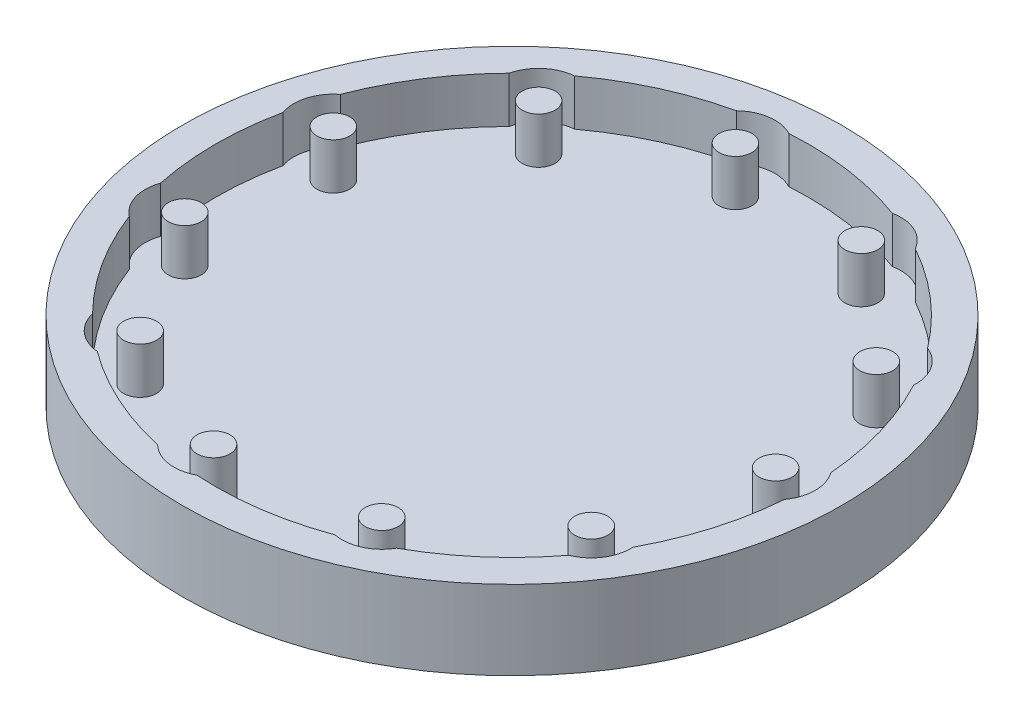
SolidWorks part; units mm, degrees
material "PET"
ref_plane "Front Plane" through (0, 0, 0) normal (0, 0, 1) x (1, 0, 0)
ref_plane "Top Plane" through (0, 0, 0) normal (0, 1, 0) x (1, 0, 0)
ref_plane "Right Plane" through (0, 0, 0) normal (1, 0, 0) x (0, 0, -1)
sketch "Sketch2" plane through (0, 0, 0) normal (0, 1, 0) x (1, 0, 0)
  circle A0 centre (0, 0) radius 50
  dimension "D1" = 100
extrude "Boss-Extrude1" add sketch "Sketch2" along normal blind 5
sketch "Sketch3" plane through (0, 5, 0) normal (0, 1, 0) x (1, 0, 0)
  line L0 (0, 0) -> (50, 0) construction
  circle A0 centre (0, 0) radius 50 construction
  circle A1 centre (40, 0) radius 2.5
  circle A2 centre (33.6501, -21.6256) radius 2.5
  circle A3 centre (16.6166, -36.3853) radius 2.5
  circle A4 centre (-5.6926, -39.5929) radius 2.5
  circle A5 centre (-26.1944, -30.23) radius 2.5
  circle A6 centre (-38.3797, -11.2693) radius 2.5
  circle A7 centre (-38.3797, 11.2693) radius 2.5
  circle A8 centre (-26.1944, 30.23) radius 2.5
  circle A9 centre (-5.6926, 39.5929) radius 2.5
  circle A10 centre (16.6166, 36.3853) radius 2.5
  circle A11 centre (33.6501, 21.6256) radius 2.5
  point P30 (0, 0)
  dimension "D2" = 5
  dimension "D1" = 40
  dimension "D3" = 11
extrude "Boss-Extrude2" add sketch "Sketch3" along normal blind 7
sketch "Sketch4" plane through (0, 5, 0) normal (0, 1, 0) x (1, 0, 0)
  arc A0 (44.8625, -3.5151) -> (44.8625, 3.5151) centre (40, 0) ccw
  arc A1 (35.8403, -27.2116) -> (39.6412, -21.2974) centre (33.6501, -21.6256) ccw
  arc A2 (15.4391, -42.2686) -> (21.834, -39.3481) centre (16.6166, -36.3853) ccw
  arc A3 (-9.8639, -43.9056) -> (-2.9053, -44.9061) centre (-5.6926, -39.5929) ccw
  arc A4 (-32.0352, -31.6029) -> (-26.7221, -36.2067) centre (-26.1944, -30.23) ccw
  arc A5 (-44.0356, -9.2665) -> (-42.0549, -16.012) centre (-38.3797, -11.2693) ccw
  arc A6 (-42.0549, 16.012) -> (-44.0356, 9.2665) centre (-38.3797, 11.2693) ccw
  arc A7 (-26.7221, 36.2067) -> (-32.0352, 31.6029) centre (-26.1944, 30.23) ccw
  arc A8 (-2.9053, 44.9061) -> (-9.8639, 43.9056) centre (-5.6926, 39.5929) ccw
  arc A9 (21.834, 39.3481) -> (15.4391, 42.2686) centre (16.6166, 36.3853) ccw
  arc A10 (39.6412, 21.2974) -> (35.8403, 27.2116) centre (33.6501, 21.6256) ccw
  arc A11 (-44.0356, 9.2665) -> (-44.0356, -9.2665) centre (0, 0) ccw
  circle A12 centre (0, 0) radius 50
  arc A13 (-32.0352, 31.6029) -> (-42.0549, 16.012) centre (0, 0) ccw
  arc A14 (-42.0549, -16.012) -> (-32.0352, -31.6029) centre (0, 0) ccw
  arc A15 (-26.7221, -36.2067) -> (-9.8639, -43.9056) centre (0, 0) ccw
  arc A16 (-2.9053, -44.9061) -> (15.4391, -42.2686) centre (0, 0) ccw
  arc A17 (21.834, -39.3481) -> (35.8403, -27.2116) centre (0, 0) ccw
  arc A18 (39.6412, -21.2974) -> (44.8625, -3.5151) centre (0, 0) ccw
  arc A19 (44.8625, 3.5151) -> (39.6412, 21.2974) centre (0, 0) ccw
  arc A20 (35.8403, 27.2116) -> (21.834, 39.3481) centre (0, 0) ccw
  arc A21 (15.4391, 42.2686) -> (-2.9053, 44.9061) centre (0, 0) ccw
  arc A22 (-9.8639, 43.9056) -> (-26.7221, 36.2067) centre (0, 0) ccw
  point P25 (0, 0)
  dimension "D1" = 12
  dimension "D3" = 90
  dimension "D4" = 100
  dimension "D2" = 11
extrude "Boss-Extrude3" add sketch "Sketch4" along normal blind 7
